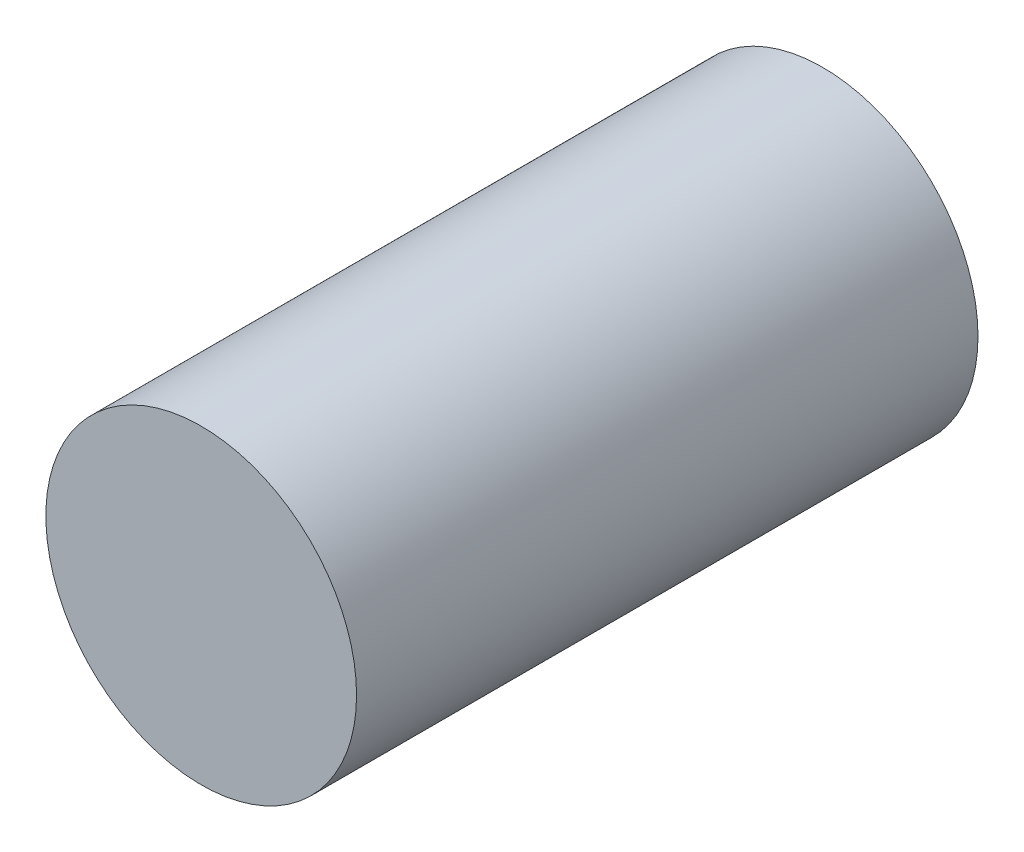
SolidWorks part; units mm, degrees
ref_plane "Front Plane" through (0, 0, 0) normal (0, 0, 1) x (1, 0, 0)
ref_plane "Top Plane" through (0, 0, 0) normal (0, 1, 0) x (1, 0, 0)
ref_plane "Right Plane" through (0, 0, 0) normal (1, 0, 0) x (0, 0, -1)
sketch "Sketch1" plane through (0, 0, 0) normal (0, 0, 1) x (1, 0, 0)
  circle A0 centre (0, 0) radius 20
extrude "Boss-Extrude1" add sketch "Sketch1" along normal blind 80 contours A0
